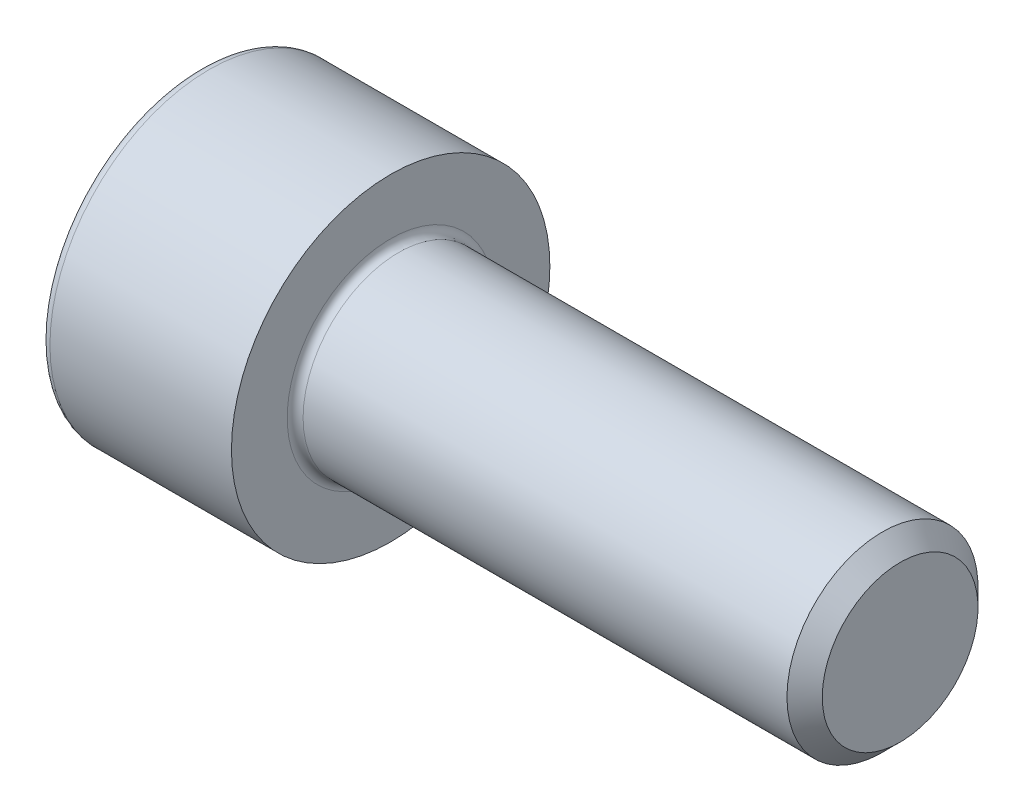
SolidWorks part; units mm, degrees
ref_plane "Plane1" through (0, 0, 0) normal (0, 0, 1) x (1, 0, 0)
ref_plane "Plane2" through (0, 0, 0) normal (0, 1, 0) x (1, 0, 0)
ref_plane "Plane3" through (0, 0, 0) normal (1, 0, 0) x (0, 0, -1)
sketch "BodySke" plane through (0, 0, 0) normal (0, 0, 1) x (1, 0, 0)
  line L0 (0, 0) -> (0, 5)
  line L1 (0, 5) -> (6, 5)
  line L2 (6, 5) -> (6, 3)
  line L3 (6, 3) -> (21.4455, 3)
  line L4 (22, 2.4455) -> (22, 0)
  line L5 (22, 0) -> (0, 0)
  line L6 (-31.75, 0) -> (127, 0) construction
  line L8 (22, 2.4455) -> (21.4455, 3)
  line L10 (22, -2.4455) -> (21.4455, -3) construction
  line L11 (7, 9.525) -> (7, 3.175) construction
  line L12 (6, 9.525) -> (6, 3.175) construction
  line L13 (-38, 9.525) -> (-38, 3.175) construction
  dimension "Diameter" = 6
  dimension "Head_ht" = 6
  dimension "Length" = 16
  dimension "Body_ch_ang" = 45
  dimension "Head_dia" = 10
  dimension "Minor_dia" = 4.891
  dimension "Advance" = 1
  dimension "Thread_nom" = 16
  dimension "Thread_length" = 60
revolve "Base-Revolve" add sketch "BodySke"
cosmetic thread "ThreadCosmetic" [suppressed]
fillet "Fillet1" radius 0.25 1 edges at (6, 0, 3)
fillet "Fillet2" radius 0.3 1 edges at (0, 0, 5)
sketch "Sketch2" plane through (0, 0, 0) normal (0, 0, 1) x (1, 0, 0)
  line L0 (0, 2.542) -> (3, 2.542)
  line L1 (3, 2.542) -> (4.4676, 0)
  line L2 (-31.75, 0) -> (127, 0) construction
  line L3 (4.4676, 0) -> (0, 0)
  line L4 (0, 0) -> (0, 2.542)
  line L6 (0, 0) -> (47.625, 0) construction
  dimension "D1" = 2.542
  dimension "D2" = 60
  dimension "Depth" = 3
revolve "Hex-PreBroach" cut sketch "Sketch2" angle 360 about L6
sketch "Sketch3" plane through (0, 0, 0) normal (-1, 0, 0) x (0, 0.5, 0.866)
  line L0 (1.4676, 2.542) -> (-1.4676, 2.542)
  line L1 (-1.4676, 2.542) -> (-2.9352, 0)
  line L2 (1.4676, 2.542) -> (2.9352, 0)
  line L3 (1.4676, -2.542) -> (2.9352, 0)
  line L4 (1.4676, -2.542) -> (-1.4676, -2.542)
  line L5 (-1.4676, -2.542) -> (-2.9352, 0)
  dimension "D1" = 2.542
  dimension "D2" = 2.542
  dimension "Hex_size" = 5.084
extrude "Hex" cut sketch "Sketch3" against normal blind 3
sketch "ThdSchSke" plane through (0, 0, 0) normal (0, 0, 1) x (1, 0, 0)
  line L0 (9, -2.4455) -> (8.6117, -3)
  line L1 (9, -2.4455) -> (9.3883, -3)
  line L2 (9.3883, -3) -> (9.3883, -3.75)
  line L3 (-3.175, 0) -> (5.1513, 0) construction
  line L4 (0, 4.7) -> (0, -4.7) construction
  line L5 (9.3883, -3.75) -> (8.6117, -3.75)
  line L6 (8.6117, -3.75) -> (8.6117, -3)
  dimension "Thread_minor" = 4.891
  dimension "Diameter" = 6
  dimension "Start" = 9
  dimension "SideAngle" = 55
  dimension "VeeAngle" = 70
  dimension "Overcut" = 7.5
revolve "ThreadSchematic" [suppressed] cut sketch "ThdSchSke" angle 360 about L3
pattern_linear "ThdSchPat" [suppressed]
equation "\"D2@Sketch3\" = \"Hex_size@Sketch3\" / 2"
equation "\"D1@Sketch3\" = \"Hex_size@Sketch3\" / 2"
equation "\"D1@Sketch2\" = \"Hex_size@Sketch3\" / 2"
equation "\"Thread_minor@ThreadCosmetic\"  =  \"Minor_dia@BodySke\""
equation "\"Depth@Sketch2\" =  \"Key_eng@Hex\""
equation "\"Thread_length@ThreadCosmetic\" = ((sgn( (\"Length@BodySke\" - \"Advance@BodySke\" * 3.0) - \"Thread_nom@BodySke\" )-1)*( (\"Length@BodySke\" - \"Advance@BodySke\" * 3.0) - \"Thread_nom@BodySke\" ))/-2+ \"Thread_nom@BodySke\""
equation "\"Thread_minor@ThdSchSke\" = \"Minor_dia@BodySke\""
equation "\"Diameter@ThdSchSke\" = \"Diameter@BodySke\""
equation "\"Overcut@ThdSchSke\" = \"Diameter@BodySke\" * 1.25"
equation "\"Start@ThdSchSke\" = \"Head_ht@BodySke\" + \"Length@BodySke\" - \"Thread_length@ThreadCosmetic\"  '---Non-countersunk---"
equation "\"Num_threads@ThdSchPat\" = int( \"Thread_length@ThreadCosmetic\" / \"Advance@BodySke\" + 0.999 )  + 1"
equation "\"Advance@ThdSchPat\" = \"Thread_length@ThreadCosmetic\" /  (\"Num_threads@ThdSchPat\" - 1) 'relax it"
equation "\"Num_threads@ThdSchPat\" = \"Num_threads@ThdSchPat\" - sgn( \"Num_threads@ThdSchPat\" - 1) '---chamfered tips only---"
